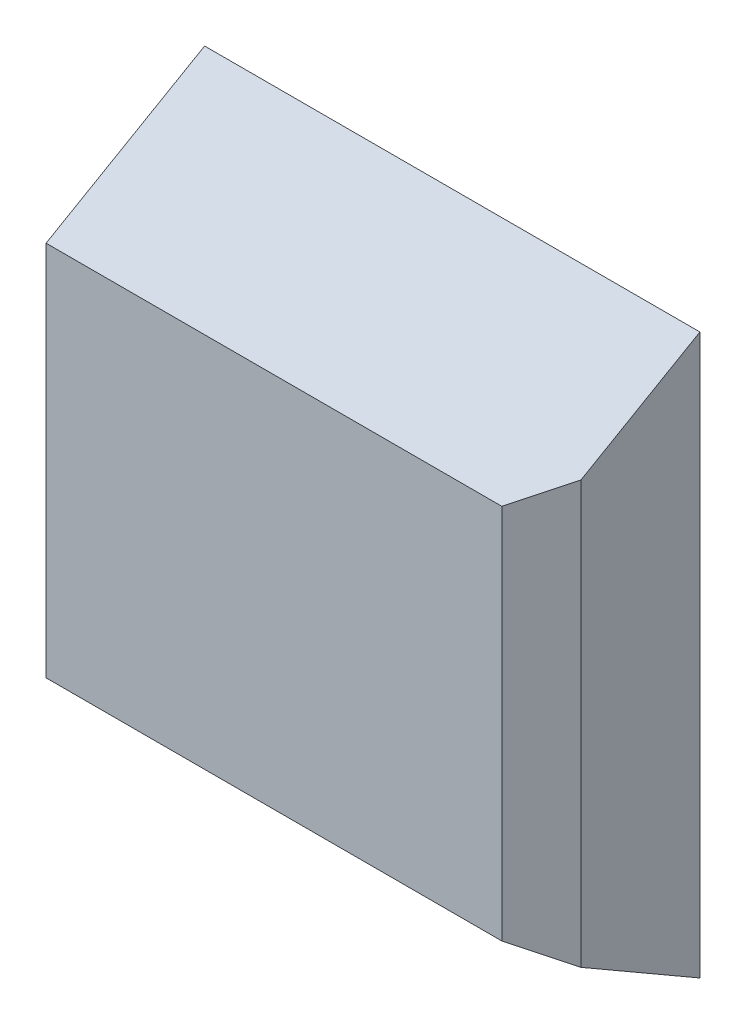
SolidWorks part; units mm, degrees
ref_plane "Front Plane" through (0, 0, 0) normal (0, 0, 1) x (1, 0, 0)
ref_plane "Top Plane" through (0, 0, 0) normal (0, 1, 0) x (1, 0, 0)
ref_plane "Right Plane" through (0, 0, 0) normal (1, 0, 0) x (0, 0, -1)
ref_plane "Plane1" through (0, 0, 4) normal (0, 0, 1) x (1, 0, 0)
sketch "Sketch1" plane through (0, 0, 4) normal (0, 0, 1) x (1, 0, 0)
  line L0 (0, 14.1188) -> (0, 0)
  line L1 (0, 0) -> (12.5, 0)
  line L2 (12.5, 0) -> (12.5, 14.1188)
  line L3 (12.5, 14.1188) -> (0, 14.1188)
extrude "Boss-Extrude1" add sketch "Sketch1" against normal blind 4
draft "Draft1" type of draft neutral plane draft angle 30 faces to draft 2 face at (6.25, 14.1188, 2) face at (6.25, 0, 2) neutral plane through (0, 0, 0) neutral plane normal (0, 0, -1) reverse direction yes parameters "D1"=30
chamfer "Chamfer1" distance 1 angle 45 1 edges at (12.5, 7.0594, 4)
